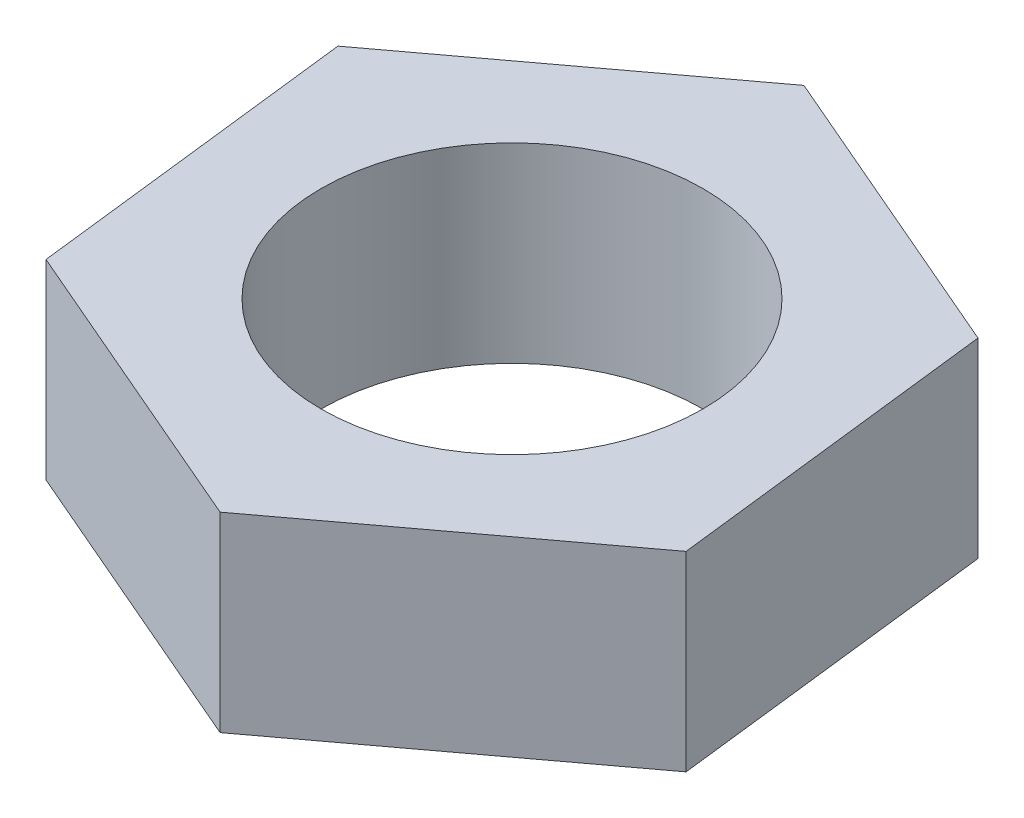
SolidWorks part; units mm, degrees
ref_plane "Plan de face" through (0, 0, 0) normal (0, 0, 1) x (1, 0, 0)
ref_plane "Plan de dessus" through (0, 0, 0) normal (0, 1, 0) x (1, 0, 0)
ref_plane "Plan de droite" through (0, 0, 0) normal (1, 0, 0) x (0, 0, -1)
sketch "Esquisse1" plane through (0, 0, 0) normal (0, 1, 0) x (1, 0, 0)
  line L9 (-16.0162, 6.9001) -> (-13.9838, -10.4204)
  line L10 (-13.9838, -10.4204) -> (2.0325, -17.3205)
  line L11 (2.0325, -17.3205) -> (16.0162, -6.9001)
  line L12 (16.0162, -6.9001) -> (13.9838, 10.4204)
  line L13 (13.9838, 10.4204) -> (-2.0325, 17.3205)
  line L14 (-2.0325, 17.3205) -> (-16.0162, 6.9001)
  circle A0 centre (0, 0) radius 15.1029 construction
  dimension "D1" = 30
extrude "Boss.-Extru.1" add sketch "Esquisse1" along normal blind 10
sketch "Esquisse2" plane through (0, 10, 0) normal (0, 1, 0) x (1, 0, 0)
  circle A0 centre (0, 0) radius 10
  dimension "D1" = 20
extrude "Enlèv. mat.-Extru.1" cut sketch "Esquisse2" against normal blind 10
cosmetic thread "Représentation de filetage1" parameters "D2"=22
